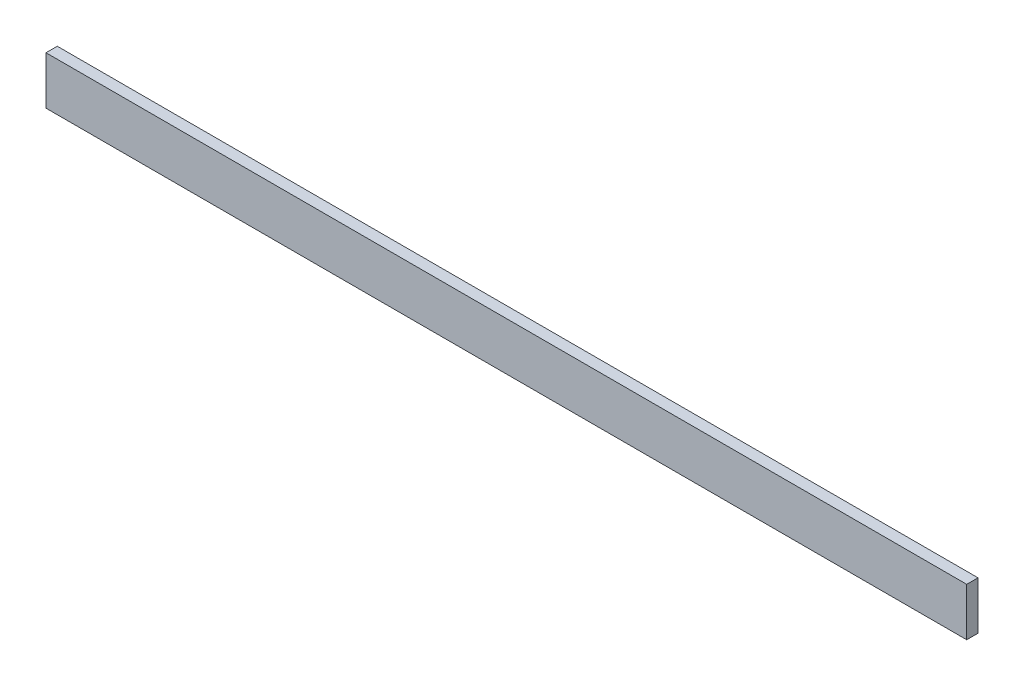
SolidWorks part; units mm, degrees
ref_plane "Front Plane" through (0, 0, 0) normal (0, 0, 1) x (1, 0, 0)
ref_plane "Top Plane" through (0, 0, 0) normal (0, 1, 0) x (1, 0, 0)
ref_plane "Right Plane" through (0, 0, 0) normal (1, 0, 0) x (0, 0, -1)
sketch "Sketch1" plane through (0, 0, 0) normal (0, 0, 1) x (1, 0, 0)
  line L0 (0, 0) -> (0, 50.8)
  line L1 (0, 0) -> (973.836, 0)
  line L2 (0, 50.8) -> (973.836, 50.8)
  line L3 (973.836, 50.8) -> (973.836, 0)
  dimension "D1" = 50.8
  dimension "D2" = 973.836
extrude "Boss-Extrude1" add sketch "Sketch1" along normal blind 11.938
